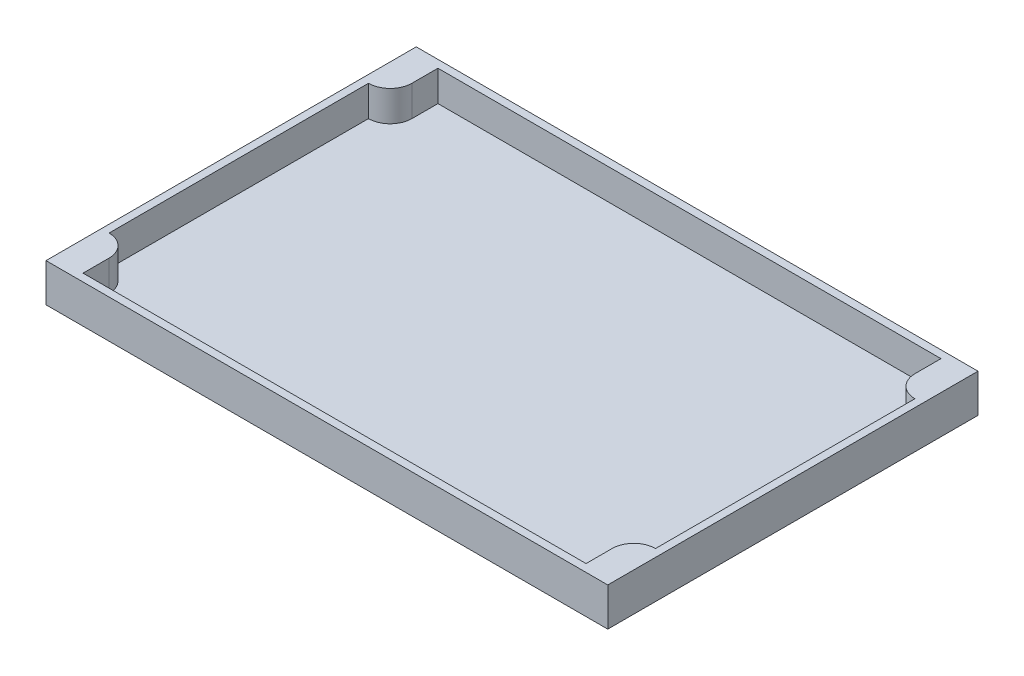
SolidWorks part; units mm, degrees
material "Acrylic (Medium-high impact)"
ref_plane "Front Plane" through (0, 0, 0) normal (0, 0, 1) x (1, 0, 0)
ref_plane "Top Plane" through (0, 0, 0) normal (0, 1, 0) x (1, 0, 0)
ref_plane "Right Plane" through (0, 0, 0) normal (1, 0, 0) x (0, 0, -1)
sketch "Sketch1" plane through (0, 0, 0) normal (0, 1, 0) x (1, 0, 0)
  line L1 (0, 0) -> (220, 0)
  line L2 (0, 0) -> (0, 145)
  line L3 (0, 145) -> (220, 145)
  line L4 (220, 0) -> (220, 145)
  dimension "D1" = 145
  dimension "D2" = 220
extrude "Boss-Extrude1" add sketch "Sketch1" along normal blind 3
sketch "Sketch2" plane through (0, 3, 0) normal (0, 1, 0) x (1, 0, 0)
  line L9 (0, 0) -> (0, 145)
  line L10 (0, 72.5) -> (3, 72.5) construction
  line L11 (3, 123.3) -> (3, 21.7)
  line L12 (11.5, 13.2) -> (11.5, 3)
  line L13 (0, 145) -> (0, 0) construction
  line L14 (0, 0) -> (220, 0) construction
  line L18 (11.5, 3) -> (208.5, 3)
  line L19 (110, 3) -> (110, 0) construction
  line L24 (220, 0) -> (0, 0)
  line L25 (110, 142) -> (110, 145) construction
  line L26 (220, 145) -> (0, 145)
  line L27 (11.5, 142) -> (208.5, 142)
  line L28 (11.5, 131.8) -> (11.5, 142)
  line L29 (220, 72.5) -> (217, 72.5) construction
  line L30 (208.5, 131.8) -> (208.5, 142)
  line L31 (208.5, 13.2) -> (208.5, 3)
  line L32 (217, 123.3) -> (217, 21.7)
  line L33 (220, 0) -> (220, 145)
  arc A4 (3, 21.7) -> (11.5, 13.2) centre (3, 13.2) cw
  arc A5 (3, 123.3) -> (11.5, 131.8) centre (3, 131.8) ccw
  arc A6 (217, 123.3) -> (208.5, 131.8) centre (217, 131.8) cw
  arc A7 (217, 21.7) -> (208.5, 13.2) centre (217, 13.2) ccw
  point P21 (0, 72.5)
  point P24 (110, 0)
  dimension "D1" = 3
  dimension "D2" = 8.5
  dimension "D3" = 18.7
extrude "Boss-Extrude2" add sketch "Sketch2" along direction (0, -1, 0) on the side of the normal offset from surface (12 mm away) 15
